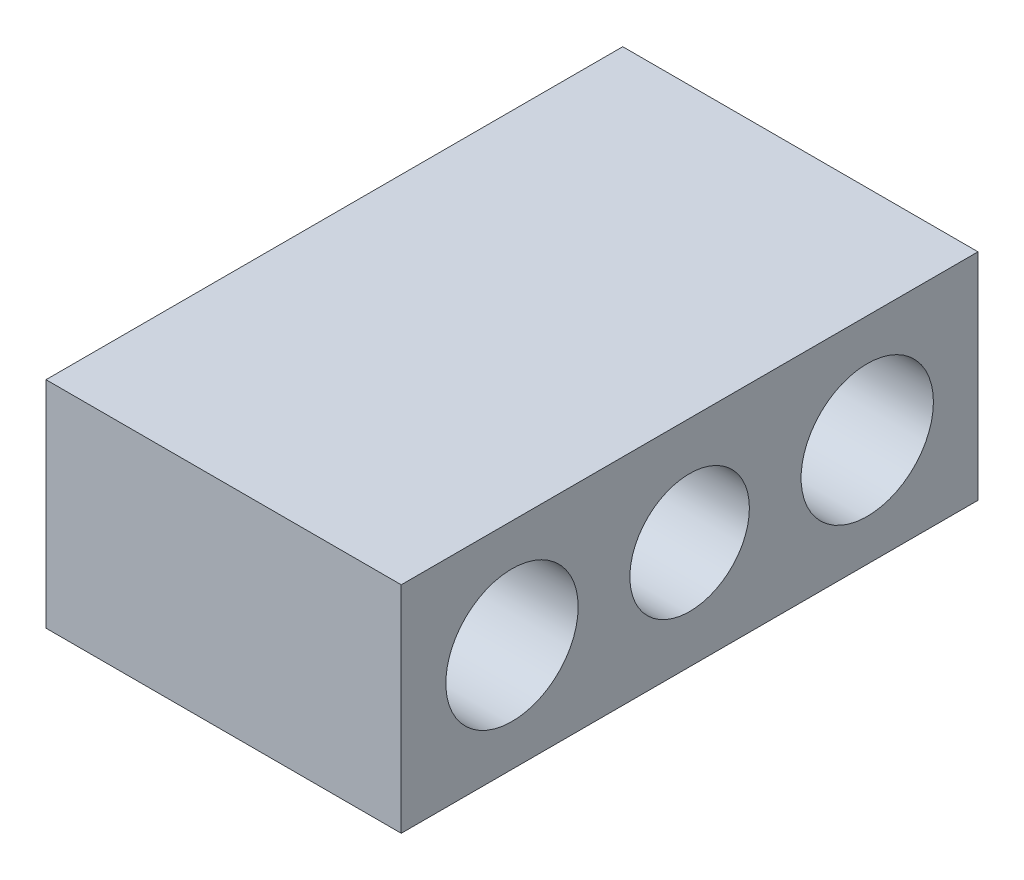
SolidWorks part; units mm, degrees
ref_plane "Front Plane" through (0, 0, 0) normal (0, 0, 1) x (1, 0, 0)
ref_plane "Top Plane" through (0, 0, 0) normal (0, 1, 0) x (1, 0, 0)
ref_plane "Right Plane" through (0, 0, 0) normal (1, 0, 0) x (0, 0, -1)
sketch "Sketch1" plane through (0, 0, 0) normal (0, 1, 0) x (1, 0, 0)
  line L1 (0, 0) -> (85, 0)
  line L2 (0, 0) -> (0, 138)
  line L3 (0, 138) -> (85, 138)
  line L4 (85, 0) -> (85, 138)
  dimension "D1" = 138
  dimension "D2" = 85
extrude "Boss-Extrude1" add sketch "Sketch1" along normal blind 51.5
sketch "Sketch3" plane through (85, 0, 0) normal (1, 0, 0) x (0, 0, -1)
  line L0 (69, 51.5) -> (69, 0) construction
  line L1 (0, 51.5) -> (138, 51.5) construction
  line L2 (0, 0) -> (138, 0) construction
  line L3 (69, 25.75) -> (111.5, 25.75) construction
  line L4 (69, 25.75) -> (26.5, 25.75) construction
  circle A0 centre (69, 25.75) radius 14.3
  circle A1 centre (26.5, 25.75) radius 15.83
  circle A2 centre (111.5, 25.75) radius 15.83
  dimension "D1" = 28.6
  dimension "D2" = 31.66
  dimension "D3" = 31.66
  dimension "D5" = 42.5
  dimension "D4" = 42.5
extrude "Cut-Extrude2" cut sketch "Sketch3" against normal up to next
sketch "Sketch4" plane through (0, 51.5, 0) normal (0, 1, 0) x (1, 0, 0)
  line L0 (85, 69) -> (0, 69) construction
  line L1 (23.05, 28.875) -> (61.95, 28.875)
  line L2 (23.05, 28.875) -> (23.05, 109.125)
  line L3 (23.05, 109.125) -> (61.95, 109.125)
  line L4 (61.95, 28.875) -> (61.95, 109.125)
  line L5 (85, 0) -> (85, 138) construction
  line L6 (0, 138) -> (0, 0) construction
  line L7 (42.5, 0) -> (42.5, 138) construction
  line L8 (0, 0) -> (85, 0) construction
  line L9 (85, 138) -> (0, 138) construction
  point P16 (61.95, 69)
  point P17 (42.5, 109.125)
  dimension "D1" = 80.25
  dimension "D2" = 38.9
